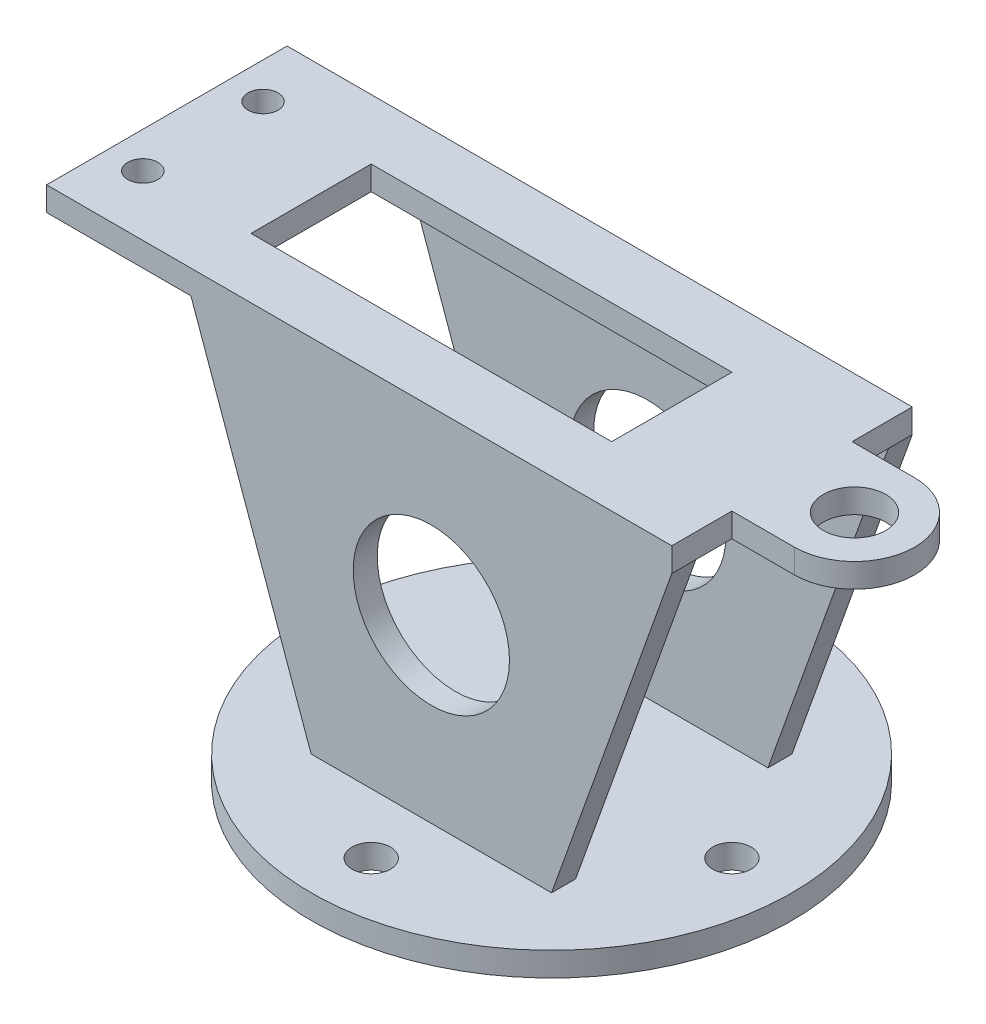
SolidWorks part; units mm, degrees
ref_plane "Front Plane" through (0, 0, 0) normal (0, 0, 1) x (1, 0, 0)
ref_plane "Top Plane" through (0, 0, 0) normal (0, 1, 0) x (1, 0, 0)
ref_plane "Right Plane" through (0, 0, 0) normal (1, 0, 0) x (0, 0, -1)
sketch "Sketch1" plane through (0, 0, 0) normal (1, 0, 0) x (0, 0, -1)
  line L0 (-20.32, 0) -> (-20.32, 71.12)
  line L1 (0, 0) -> (0, 71.12) construction
  line L2 (-20.32, 0) -> (-25.4, 0)
  line L3 (-25.4, 0) -> (-25.4, 71.12)
  line L4 (-25.4, 71.12) -> (-25.4, 76.2)
  line L5 (-25.4, 76.2) -> (25.4, 76.2)
  line L6 (0, 76.2) -> (0, 71.12)
  line L7 (20.32, 71.12) -> (-20.32, 71.12)
  line L8 (25.4, 71.12) -> (25.4, 76.2)
  line L9 (25.4, 0) -> (25.4, 71.12)
  line L10 (20.32, 0) -> (25.4, 0)
  line L11 (20.32, 0) -> (20.32, 71.12)
  dimension "D1" = 20.32
  dimension "D2" = 25.4
  dimension "D3" = 71.12
  dimension "D4" = 5.08
extrude "Boss-Extrude1" add sketch "Sketch1" along normal mid plane 101.6 contours L7 L6 L5 L4 L3 L2 L0 | L11 L10 L9 L8 L5 L6 L7
sketch "Sketch2" plane through (0, 76.2, 0) normal (0, 1, 0) x (1, 0, 0)
  line L0 (50.8, -25.4) -> (50.8, 25.4) construction
  line L1 (-50.8, 25.4) -> (-81.28, 25.4)
  line L2 (-50.8, 25.4) -> (-50.8, -25.4)
  line L3 (-50.8, -25.4) -> (-81.28, -25.4)
  line L4 (-81.28, 25.4) -> (-81.28, -25.4)
  line L5 (50.8, 12.7) -> (64.008, 12.7)
  line L6 (50.8, 12.7) -> (50.8, -12.7)
  line L7 (50.8, -12.7) -> (64.008, -12.7)
  line L8 (-81.28, 0) -> (-50.8, 0) construction
  circle A0 centre (64.008, 0) radius 12.7
  circle A1 centre (64.008, 0) radius 6.604
  circle A2 centre (-73.66, 12.7) radius 3.175
  circle A3 centre (-73.66, -12.7) radius 3.175
  point P11 (50.8, 0)
  point P22 (0, 0)
  line M6 (-50.8, 25.4) -> (-50.8, -25.4)
  line M8 (50.8, -25.4) -> (50.8, 25.4)
  dimension "D4" = 25.4
  dimension "D2" = 13.208
  dimension "D3" = 6.35
  dimension "D1" = 30.48
  dimension "D5" = 13.208
  dimension "D6" = 25.4
  dimension "D7" = 12.7
  dimension "D8" = 50.8
  dimension "D9" = 7.62
extrude "Boss-Extrude2" add sketch "Sketch2" against normal up to surface (5.08 mm away) contours L1 L4 L3 M6 | A0 A1 | A0 L5 L7 M8 | L8 L4 L3 L2 A3
sketch "Sketch3" plane through (0, 76.2, 0) normal (0, 1, 0) x (1, 0, 0)
  line L0 (50.8, 25.4) -> (-81.28, 25.4) construction
  line L1 (-50.8, 12.7) -> (25.4, 12.7)
  line L2 (-50.8, 12.7) -> (-50.8, -12.7)
  line L3 (-50.8, -12.7) -> (25.4, -12.7)
  line L4 (25.4, 12.7) -> (25.4, -12.7)
  line L5 (-81.28, 25.4) -> (-81.28, -25.4) construction
  point P4 (-50.8, 0)
  dimension "D1" = 25.4
  dimension "D2" = 25.4
  dimension "D3" = 76.2
  dimension "D4" = 30.48
extrude "Cut-Extrude1" cut sketch "Sketch3" against normal through all
sketch "Sketch4" plane through (0, 0, 0) normal (0, -1, 0) x (-1, 0, 0)
  circle A0 centre (0, 0) radius 50.8
  circle A1 centre (0, 0) radius 38.1
  circle A2 centre (0, -38.1) radius 4.064
  circle A3 centre (-38.1, 0) radius 4.064
  circle A4 centre (0, 38.1) radius 4.064
  circle A5 centre (38.1, 0) radius 4.064
  point P15 (0, 0)
  line M2 (50.8, -20.32) -> (-50.8, -20.32)
  line M4 (-50.8, -25.4) -> (50.8, -25.4)
  dimension "D1" = 101.6
  dimension "D2" = 76.2
  dimension "D3" = 8.128
  dimension "D4" = 4
sketch "Sketch5" plane through (0, 0, 25.4) normal (0, 0, 1) x (1, 0, 0)
  line L0 (-50.8, 71.12) -> (-25.4, 0)
  line L1 (-50.8, 0) -> (50.8, 0) construction
  line L2 (-25.4, 0) -> (25.4, 0)
  line L3 (25.4, 0) -> (50.8, 71.12)
  line L4 (-50.8, 71.12) -> (-50.8, 0)
  line L5 (-50.8, 0) -> (-25.4, 0)
  line L6 (25.4, 0) -> (50.8, 0)
  line L7 (50.8, 0) -> (50.8, 71.12)
  point P5 (0, 0)
  line M2 (-50.8, 71.12) -> (-50.8, 0)
  line M3 (-50.8, 0) -> (50.8, 0)
  line M4 (50.8, 0) -> (50.8, 76.2)
  dimension "D1" = 50.8
extrude "Cut-Extrude2" cut sketch "Sketch5" against normal through all contours L0 M2 M3 | L3 M3 M4
extrude "Boss-Extrude3" add sketch "Sketch4" along normal blind 5.08 contours A2 A1 A0 M4 | A5 A1 A0 A3 A4 M2 | A5 A1 A4 A3 M2 | A1 A0 M4 M2 | A1 A0 M2 M4 | A2 A1 M4 | A1 M2 M4
sketch "Sketch6" plane through (0, 0, 25.4) normal (0, 0, 1) x (1, 0, 0)
  circle A0 centre (0, 38.1) radius 16.51
  dimension "D1" = 33.02
  dimension "D2" = 38.1
extrude "Cut-Extrude3" cut sketch "Sketch6" against normal through all
